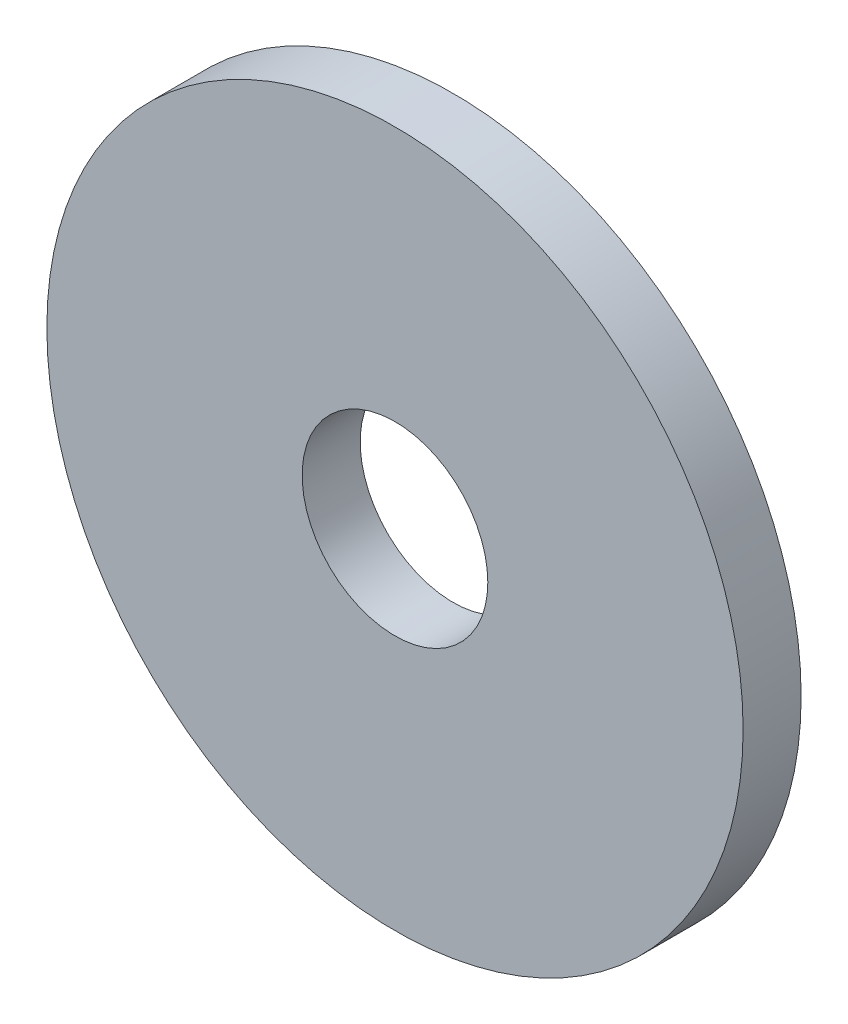
SolidWorks part; units mm, degrees
ref_plane "Front Plane" through (0, 0, 0) normal (0, 0, 1) x (1, 0, 0)
ref_plane "Top Plane" through (0, 0, 0) normal (0, 1, 0) x (1, 0, 0)
ref_plane "Right Plane" through (0, 0, 0) normal (1, 0, 0) x (0, 0, -1)
sketch "Sketch1" plane through (0, 0, 0) normal (0, 0, 1) x (1, 0, 0)
  circle A0 centre (0, 0) radius 9.525
  circle A1 centre (0, 0) radius 2.54
  dimension "D1" = 19.05
  dimension "D2" = 5.08
extrude "Boss-Extrude1" add sketch "Sketch1" along normal blind 1.5875
